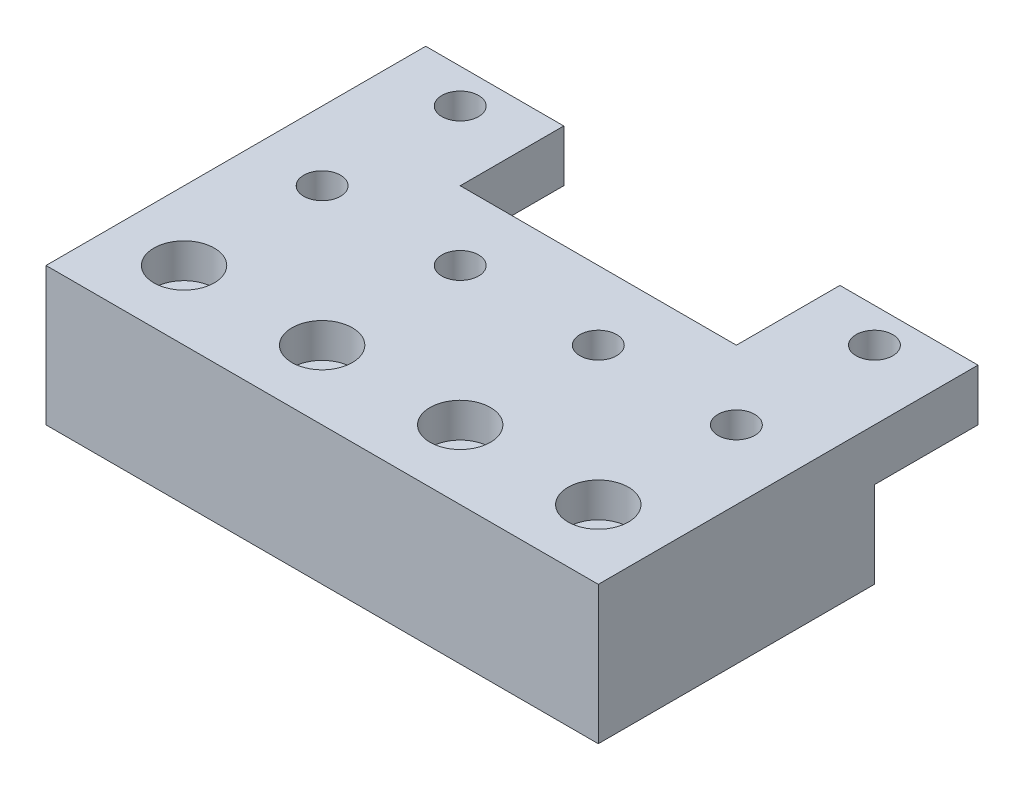
SolidWorks part; units mm, degrees
ref_plane "Front Plane" through (0, 0, 0) normal (0, 0, 1) x (1, 0, 0)
ref_plane "Top Plane" through (0, 0, 0) normal (0, 1, 0) x (1, 0, 0)
ref_plane "Right Plane" through (0, 0, 0) normal (1, 0, 0) x (0, 0, -1)
sketch "Sketch1" plane through (0, 0, 0) normal (0, 1, 0) x (1, 0, 0)
  line L1 (0, 0) -> (101.6, 0)
  line L2 (0, 0) -> (0, 50.8)
  line L3 (0, 50.8) -> (101.6, 50.8)
  line L4 (101.6, 0) -> (101.6, 50.8)
extrude "Boss-Extrude1" add sketch "Sketch1" along normal blind 25.4
hole_wizard "CBORE for 1/4 Socket Head Cap Screw1" positions "Sketch4" profile "Sketch3" counterbore size "1/4" standard "Ansi Inch" end condition through all
sketch "Sketch4" plane through (0, 25.4, 0) normal (0, 1, 0) x (-1, 0, 0)
  point P0 (-12.7, -12.7)
sketch "Sketch3" plane through (12.7, 25.4, -12.7) normal (1, 0, 0) x (0, 0, 1)
  line L0 (0, 0) -> (0, 25.4)
  line L1 (0, 25.4) -> (3.3782, 25.4)
  line L3 (3.3782, 25.4) -> (3.3782, 6.35)
  line L4 (3.3782, 6.35) -> (5.5562, 6.35)
  line L5 (5.5562, 6.35) -> (5.5563, 0)
  line L7 (5.5563, 0) -> (0, 0)
  line L11 (0, -6.35) -> (0, 107.95) construction
  dimension "Thru Hole Dia." = 6.7564
  dimension "Thru Hole Depth" = 25.4
  dimension "C'Bore Dia." = 11.1125
  dimension "C'Bore Depth" = 6.35
pattern_linear "LPattern1" count 1 spacing 25.4 along (0, 0, 1) count 4 spacing 25.4 along (1, 0, 0) of "CBORE for 1/4 Socket Head Cap Screw1"
hole_wizard "1/4 Clearance Hole1" positions "Sketch6" profile "Sketch5" hole size "1/4" standard "Ansi Inch" end condition through all
sketch "Sketch6" plane through (0, 25.4, 0) normal (0, 1, 0) x (-1, 0, 0)
  point P0 (-12.7, -38.1)
sketch "Sketch5" plane through (12.7, 25.4, -38.1) normal (1, 0, 0) x (0, 0, 1)
  line L0 (0, 0) -> (0, 25.4)
  line L1 (0, 25.4) -> (3.3782, 25.4)
  line L2 (3.3782, 25.4) -> (3.3782, 0)
  line L5 (3.3782, 0) -> (0, 0)
  line L11 (0, -6.35) -> (0, 107.95) construction
  dimension "Thru Hole Dia." = 6.7564
  dimension "Thru Hole Depth" = 25.4
pattern_linear "LPattern2" count 4 spacing 25.4 along (1, 0, 0) of "1/4 Clearance Hole1"
sketch "Sketch7" plane through (0, 0, -50.8) normal (0, 0, -1) x (-1, 0, 0)
  line L0 (0, 25.4) -> (0, 0) construction
  line L1 (-101.6, 25.4) -> (0, 25.4)
  line L2 (-101.6, 25.4) -> (-101.6, 15.875)
  line L3 (-101.6, 15.875) -> (0, 15.875)
  line L4 (0, 25.4) -> (0, 15.875)
extrude "Boss-Extrude2" add sketch "Sketch7" along normal blind 19.05
sketch "Sketch8" plane through (0, 0, -69.85) normal (0, 0, -1) x (-1, 0, 0)
  line L0 (0, 25.4) -> (-101.6, 25.4) construction
  line L1 (-76.2, 25.4) -> (-25.4, 25.4)
  line L2 (-76.2, 25.4) -> (-76.2, 15.875)
  line L3 (-76.2, 15.875) -> (-25.4, 15.875)
  line L4 (-25.4, 25.4) -> (-25.4, 15.875)
  line L5 (-101.6, 15.875) -> (0, 15.875) construction
extrude "Cut-Extrude1" cut sketch "Sketch8" against normal blind 19.05
pattern_linear "LPattern3" count 2 spacing 25.4 along (0, 0, -1) of "1/4 Clearance Hole1"
pattern_linear "LPattern4" count 2 spacing 76.2 along (1, 0, 0) of "LPattern3"
